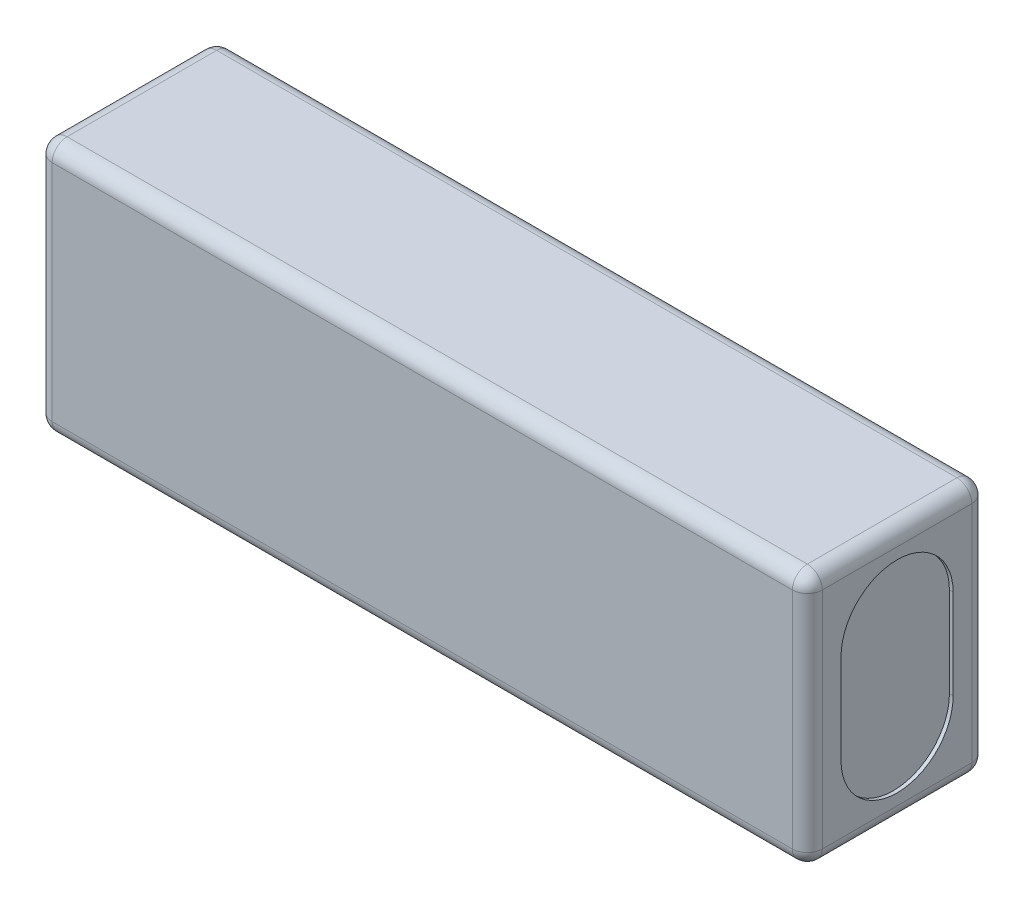
SolidWorks part; units mm, degrees
ref_plane "Plano frontal" through (0, 0, 0) normal (0, 0, 1) x (1, 0, 0)
ref_plane "Plano superior" through (0, 0, 0) normal (0, 1, 0) x (1, 0, 0)
ref_plane "Plano direito" through (0, 0, 0) normal (1, 0, 0) x (0, 0, -1)
sketch "Esboço1" plane through (0, 0, 0) normal (0, 0, 1) x (1, 0, 0)
  line L1 (-51.5, 17) -> (51.5, 17)
  line L2 (-51.5, 17) -> (-51.5, -17)
  line L3 (-51.5, -17) -> (51.5, -17)
  line L4 (51.5, 17) -> (51.5, -17)
  line L5 (-51.5, 17) -> (51.5, -17) construction
  line L6 (-51.5, -17) -> (51.5, 17) construction
  point P0 (0, 0)
  dimension "D1" = 103
  dimension "D2" = 34
extrude "Ressalto-extrusão1" add sketch "Esboço1" along normal blind 24
sketch "Esboço2" plane through (51.5, 0, 0) normal (1, 0, 0) x (0, 0, -1)
  line L0 (-12, 17) -> (-12, -17) construction
  line L1 (-24, 17) -> (0, 17) construction
  line L2 (-24, -17) -> (0, -17) construction
  line L3 (0, 0) -> (-24, 0) construction
  line L4 (-24, -17) -> (-24, 17) construction
  line L5 (-12, 6) -> (-12, -6) construction
  line L6 (-4.5, 6) -> (-4.5, -6)
  line L7 (-19.5, 6) -> (-19.5, -6)
  arc A0 (-4.5, 6) -> (-19.5, 6) centre (-12, 6) ccw
  arc A1 (-19.5, -6) -> (-4.5, -6) centre (-12, -6) ccw
  point P13 (-12, 0)
  dimension "D1" = 12
  dimension "D2" = 15
extrude "Corte-extrusão1" cut sketch "Esboço2" against normal blind 0.5
mirror "Espelhar1" about plane through (0, 0, 0) normal (1, 0, 0) of "Corte-extrusão1"
fillet "Filete1" radius 2 12 edges at (-51.5, -17, 12) (51.5, -17, 12) (-51.5, 0, 0) (0, -17, 0) (51.5, 0, 0) (51.5, 17, 12) (-51.5, 17, 12) (0, 17, 0) (0, -17, 24) (-51.5, 0, 24) (0, 17, 24) (51.5, 0, 24)
